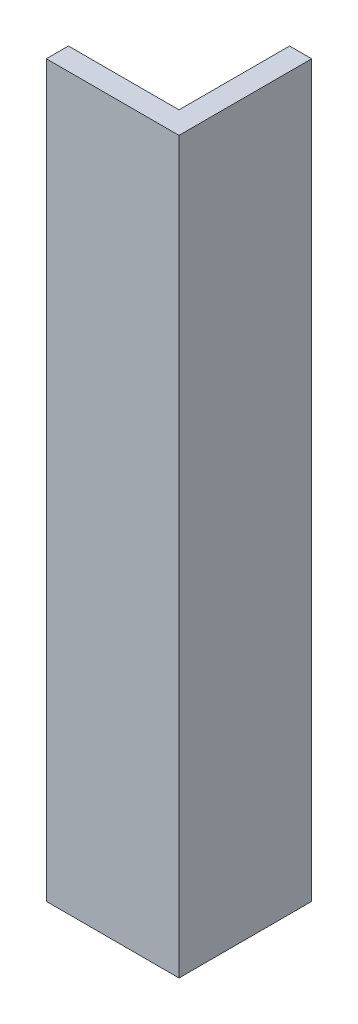
SolidWorks part; units mm, degrees
ref_plane "Front Plane" through (0, 0, 0) normal (0, 0, 1) x (1, 0, 0)
ref_plane "Top Plane" through (0, 0, 0) normal (0, 1, 0) x (1, 0, 0)
ref_plane "Right Plane" through (0, 0, 0) normal (1, 0, 0) x (0, 0, -1)
sketch "Sketch1" plane through (0, 0, 0) normal (0, 1, 0) x (1, 0, 0)
  line L1 (0, 0) -> (15.24, 0)
  line L2 (0, 0) -> (0, 2.54)
  line L3 (0, 2.54) -> (12.7, 2.54)
  line L4 (15.24, 0) -> (15.24, 2.54)
  line L5 (15.24, 0) -> (12.9637, 0)
  line L6 (15.24, 0) -> (15.24, 15.24)
  line L7 (15.24, 15.24) -> (12.7, 15.24)
  line L8 (12.7, 2.54) -> (12.7, 15.24)
  dimension "D1" = 12.7
  dimension "D2" = 12.7
  dimension "D3" = 2.54
  dimension "D4" = 2.54
extrude "Boss-Extrude1" add sketch "Sketch1" along normal blind 83.82 contours L8 L3 L2 L1 L4 L6 L7
